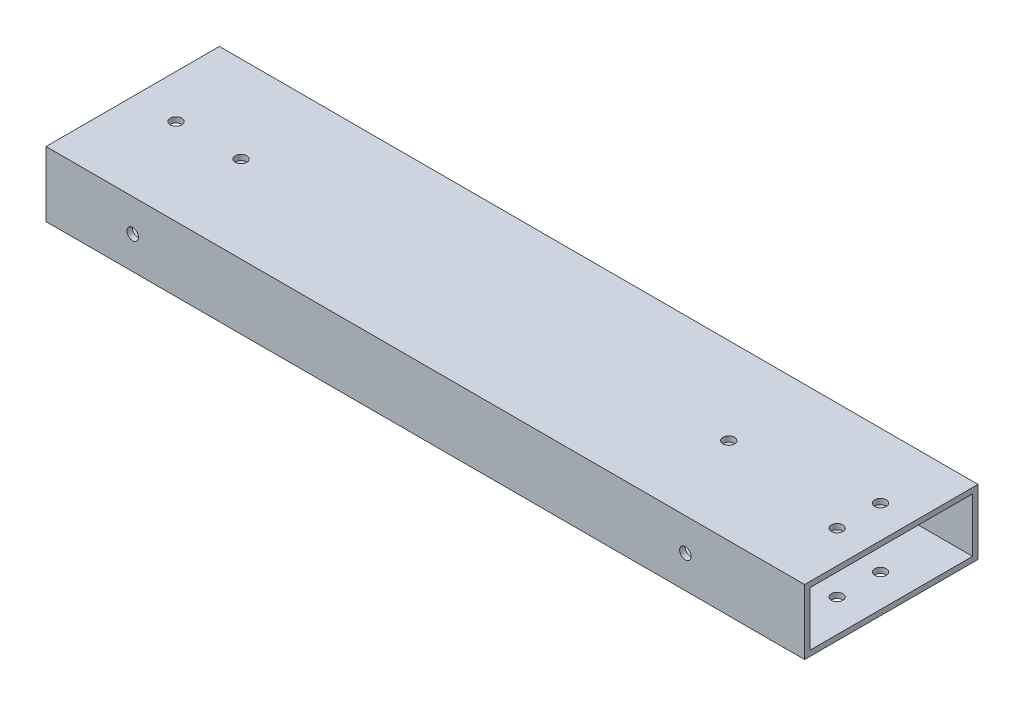
SolidWorks part; units mm, degrees
ref_plane "Front Plane" through (0, 0, 0) normal (0, 0, 1) x (1, 0, 0)
ref_plane "Top Plane" through (0, 0, 0) normal (0, 1, 0) x (1, 0, 0)
ref_plane "Right Plane" through (0, 0, 0) normal (1, 0, 0) x (0, 0, -1)
sketch "Sketch1" plane through (0, 0, 0) normal (1, 0, 0) x (0, 0, -1)
  line L1 (-50.8, -19.05) -> (50.8, -19.05)
  line L2 (-50.8, -19.05) -> (-50.8, 19.05)
  line L3 (-50.8, 19.05) -> (50.8, 19.05)
  line L4 (50.8, -19.05) -> (50.8, 19.05)
  line L5 (-50.8, -19.05) -> (50.8, 19.05) construction
  line L6 (-50.8, 19.05) -> (50.8, -19.05) construction
  line L7 (47.625, -15.875) -> (-47.625, -15.875)
  line L8 (47.625, -15.875) -> (47.625, 15.875)
  line L9 (47.625, 15.875) -> (-47.625, 15.875)
  line L10 (-47.625, -15.875) -> (-47.625, 15.875)
  line L11 (47.625, -15.875) -> (-47.625, 15.875) construction
  line L12 (47.625, 15.875) -> (-47.625, -15.875) construction
  point P0 (0, 0)
  point P6 (0, 0)
  dimension "D1" = 3.175
  dimension "D2" = 101.6
  dimension "D3" = 38.1
  dimension "D4" = 3.175
extrude "Boss-Extrude1" add sketch "Sketch1" along normal blind 444.5 contours L1 L4 L3 L2 L7 L10 L9 L8
hole_wizard "H (0.266) Diameter Hole1" positions "Sketch2" profile "Sketch4" hole size "H" standard "ANSI Inch" end condition through all
sketch "Sketch2" plane through (0, 19.05, 0) normal (0, 1, 0) x (1, 0, 0)
  line L0 (425.45, 12.7) -> (425.45, -12.7) construction
  point P0 (25.4, 0)
  point P2 (63.5, 0)
  point P4 (349.25, 0)
  point P6 (425.45, 12.7)
  point P8 (425.45, -12.7)
  point P14 (425.45, 0)
  dimension "D1" = 25.4
  dimension "D2" = 38.1
  dimension "D3" = 25.4
  dimension "D4" = 76.2
  dimension "D5" = 285.75
sketch "Sketch4" plane through (25.4, 19.05, 0) normal (1, 0, 0) x (0, 0, 1)
  line L0 (0, 0) -> (0, 38.1)
  line L1 (0, 38.1) -> (3.3782, 38.1)
  line L2 (3.3782, 38.1) -> (3.3782, 0)
  line L5 (3.3782, 0) -> (0, 0)
  line L11 (0, -6.35) -> (0, 107.95) construction
  dimension "Thru Hole Dia." = 6.7564
  dimension "Thru Hole Depth" = 38.1
hole_wizard "H (0.266) Diameter Hole2" positions "Sketch7" profile "Sketch6" hole size "H" standard "ANSI Inch" end condition through all
sketch "Sketch7" plane through (0, 0, -50.8) normal (0, 0, -1) x (-1, 0, 0)
  point P0 (-50.8, 0)
  point P2 (-374.65, 0)
  dimension "D1" = 50.8
  dimension "D2" = 374.65
sketch "Sketch6" plane through (50.8, 0, -50.8) normal (1, 0, 0) x (0, 1, 0)
  line L0 (0, 0) -> (0, 101.6)
  line L1 (0, 101.6) -> (3.3782, 101.6)
  line L2 (3.3782, 101.6) -> (3.3782, 0)
  line L5 (3.3782, 0) -> (0, 0)
  line L11 (0, -6.35) -> (0, 107.95) construction
  dimension "Thru Hole Dia." = 6.7564
  dimension "Thru Hole Depth" = 101.6
